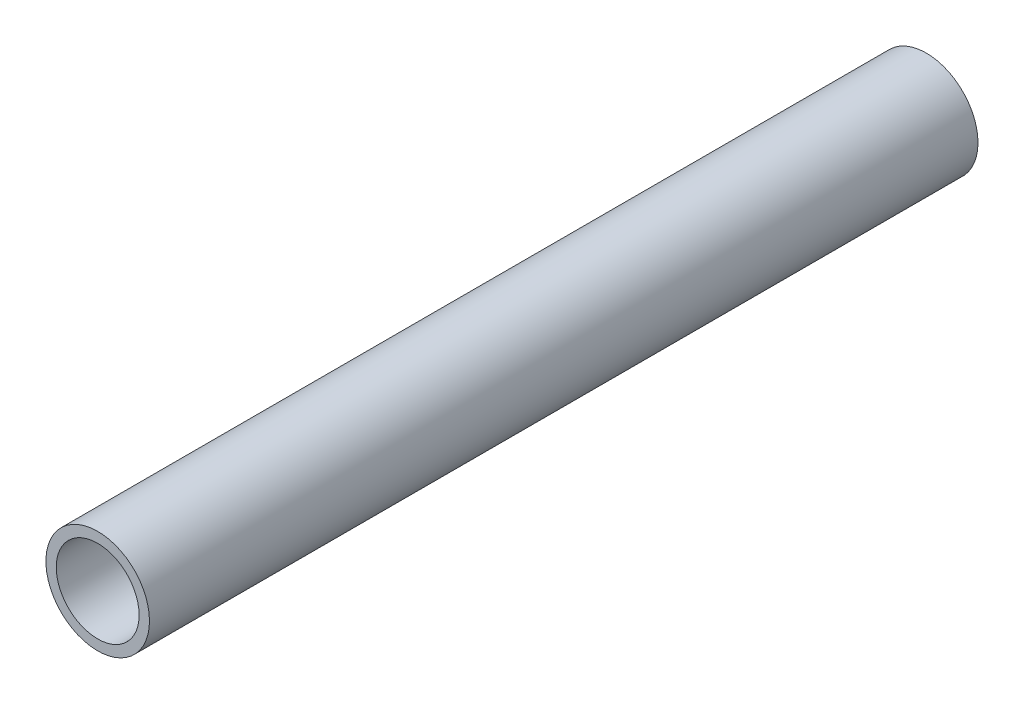
SolidWorks part; units mm, degrees
material "PVC Rigid"
ref_plane "Front Plane" through (0, 0, 0) normal (0, 0, 1) x (1, 0, 0)
ref_plane "Top Plane" through (0, 0, 0) normal (0, 1, 0) x (1, 0, 0)
ref_plane "Right Plane" through (0, 0, 0) normal (1, 0, 0) x (0, 0, -1)
sketch "Sketch1" plane through (0, 0, 0) normal (0, 0, 1) x (1, 0, 0)
  circle A0 centre (0, 0) radius 12.7
  circle A1 centre (0, 0) radius 10.16
  dimension "D1" = 25.4
  dimension "D2" = 20.32
extrude "Boss-Extrude1" add sketch "Sketch1" along normal blind 203.2
